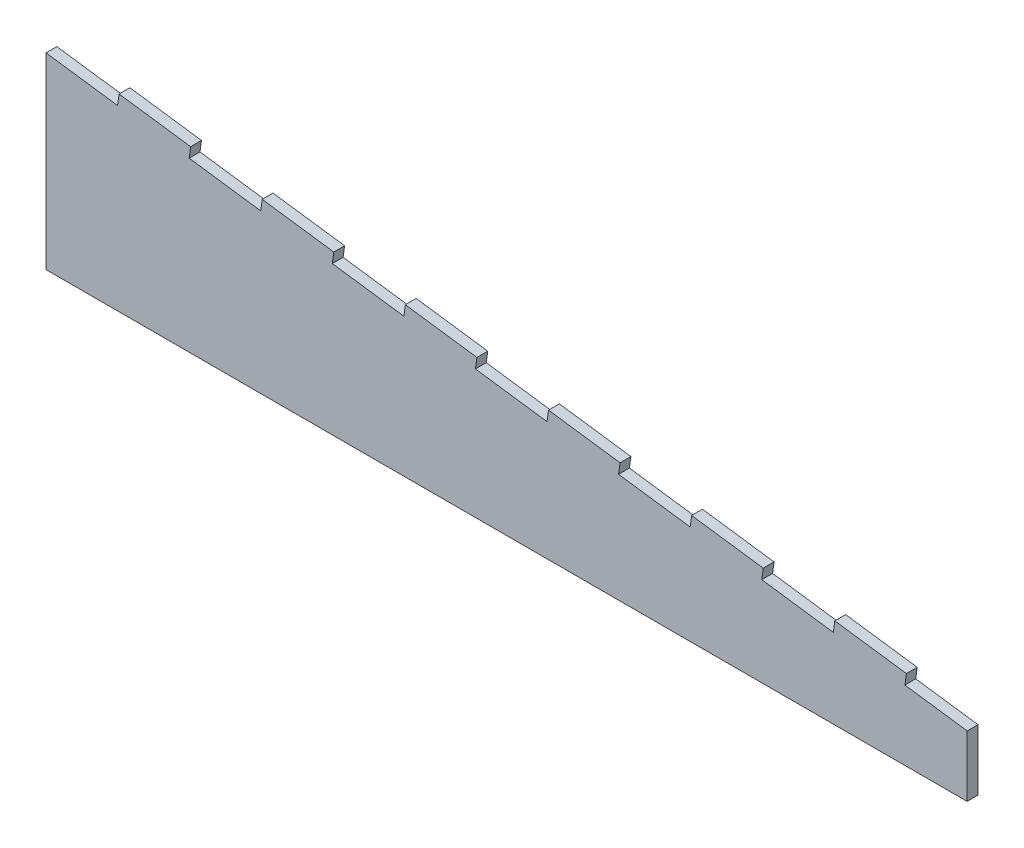
SolidWorks part; units mm, degrees
ref_plane "Plan de face" through (0, 0, 0) normal (0, 0, 1) x (1, 0, 0)
ref_plane "Plan de dessus" through (0, 0, 0) normal (0, 1, 0) x (1, 0, 0)
ref_plane "Plan de droite" through (0, 0, 0) normal (1, 0, 0) x (0, 0, -1)
sketch "Esquisse1" plane through (0, 0, 0) normal (0, 0, 1) x (1, 0, 0)
  line L0 (0, 0) -> (-255, 0)
  line L1 (-255, 0) -> (-255, 55)
  line L2 (-255, 55) -> (0, 19.9375)
  line L3 (0, 19.9375) -> (0, 0)
  line L4 (0, 19.9375) -> (145, 0) construction
  line L5 (145, 0) -> (0, 0) construction
  point P5 (143.1441, 0)
  dimension "D1" = 55
  dimension "D2" = 400
  dimension "D3" = 145
extrude "Boss.-Extru.1" add sketch "Esquisse1" along normal blind 3
sketch "Esquisse2" plane through (0, 0, 3) normal (0, 0, 1) x (1, 0, 0)
  line L0 (-255, 51.9718) -> (0, 16.9093) construction
  line L1 (-255, 55) -> (-255, 0) construction
  line L2 (0, 0) -> (0, 19.9375) construction
  line L3 (0, 19.9375) -> (-255, 55) construction
  line L4 (-234.7778, 52.2194) -> (-235.1864, 49.2474)
  line L5 (-235.1864, 49.2474) -> (-215.3728, 46.523)
  line L6 (-215.3728, 46.523) -> (-214.9642, 49.4951)
  line L7 (-214.9642, 49.4951) -> (-195.1506, 46.7707)
  line L8 (-195.1506, 46.7707) -> (-195.5593, 43.7987)
  line L9 (-195.5593, 43.7987) -> (-175.7457, 41.0743)
  line L10 (-175.7457, 41.0743) -> (-175.337, 44.0463)
  line L11 (-175.337, 44.0463) -> (-155.5235, 41.322)
  line L12 (-155.5235, 41.322) -> (-155.9321, 38.3499)
  line L13 (-155.9321, 38.3499) -> (-136.1185, 35.6256)
  line L14 (-136.1185, 35.6256) -> (-135.7099, 38.5976)
  line L15 (-135.7099, 38.5976) -> (-115.8963, 35.8732)
  line L16 (-115.8963, 35.8732) -> (-116.305, 32.9012)
  line L17 (-116.305, 32.9012) -> (-96.4914, 30.1768)
  line L18 (-96.4914, 30.1768) -> (-96.0827, 33.1489)
  line L19 (-96.0827, 33.1489) -> (-76.2692, 30.4245)
  line L20 (-76.2692, 30.4245) -> (-76.6778, 27.4525)
  line L21 (-76.6778, 27.4525) -> (-56.8642, 24.7281)
  line L22 (-56.8642, 24.7281) -> (-56.4556, 27.7001)
  line L23 (-234.7778, 52.2194) -> (-255, 55)
  line L24 (-255, 55) -> (-255, 51.9718)
  line L25 (-255, 51.9718) -> (-254.5913, 54.9438) construction
  line L26 (-56.4556, 27.7001) -> (-36.642, 24.9758)
  line L27 (-36.642, 24.9758) -> (-37.0507, 22.0037)
  line L28 (-37.0507, 22.0037) -> (-17.2371, 19.2794)
  line L29 (-17.2371, 19.2794) -> (-16.8284, 22.2514)
  line L30 (-16.8284, 22.2514) -> (0, 19.9375)
  line L31 (0, 19.9375) -> (0, 16.9093)
  line L32 (0, 16.9093) -> (-17.2371, 19.2794)
  line L33 (-37.0507, 22.0037) -> (-56.8642, 24.7281)
  line L34 (-76.6778, 27.4525) -> (-96.4914, 30.1768)
  line L35 (-116.305, 32.9012) -> (-136.1185, 35.6256)
  line L36 (-155.9321, 38.3499) -> (-175.7457, 41.0743)
  line L37 (-195.5593, 43.7987) -> (-215.3728, 46.523)
  line L38 (-235.1864, 49.2474) -> (-255, 51.9718)
  line M14 (0, 0) -> (0, 19.9375)
  line M15 (0, 19.9375) -> (-255, 55)
  line M16 (-255, 55) -> (-255, 0)
  dimension "D1" = 3
  dimension "D2" = 20
  dimension "D3" = 20
  dimension "D4" = 20
extrude "Enlèv. mat.-Extru.1" cut sketch "Esquisse2" against normal through all contours L38 L4 M15 M16 | L37 L8 L6 M15 | L36 L12 L10 M15 | L35 L16 L14 M15 | L34 L20 L18 M15 | L33 L27 L22 M15 | L32 L29 M14 M15
